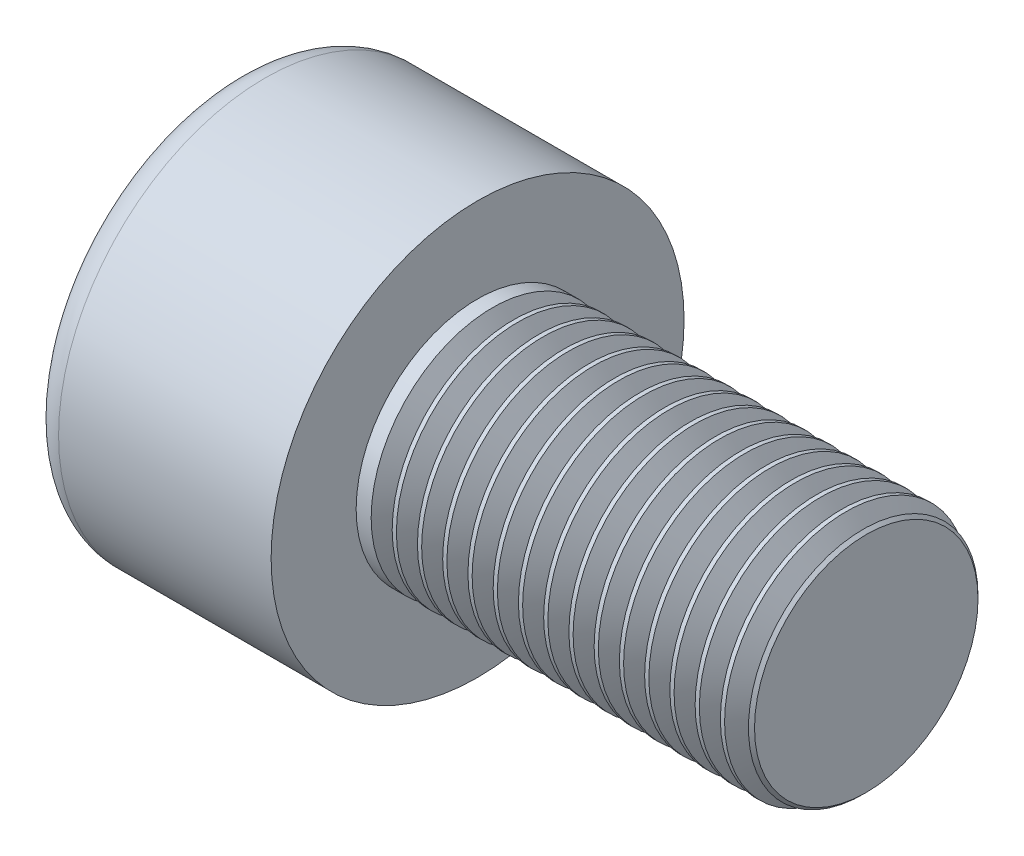
SolidWorks part; units mm, degrees
ref_plane "Front" through (0, 0, 0) normal (0, 0, 1) x (1, 0, 0)
ref_plane "Top" through (0, 0, 0) normal (0, 1, 0) x (1, 0, 0)
ref_plane "Right" through (0, 0, 0) normal (1, 0, 0) x (0, 0, -1)
sketch "Sketch1" plane through (0, 0, 0) normal (1, 0, 0) x (0, 0, -1)
  circle A0 centre (0, 0) radius 4.25
  dimension "dk" = 8.5
extrude "BaseHead" add sketch "Sketch1" along normal blind 5
sketch "Sketch2" plane through (5, 0, 0) normal (1, 0, 0) x (0, 0, -1)
  circle A0 centre (0, 0) radius 2.5
  dimension "d" = 5
extrude "BaseBody" add sketch "Sketch2" along normal blind 8
cosmetic thread "ThreadCosmetic1" parameters "b"=16, "D2"=4.134
sketch "Sketch3" plane through (0, 0, 0) normal (1, 0, 0) x (0, 0, -1)
  line L1 (2.3094, 0) -> (1.1547, 2)
  line L2 (1.1547, 2) -> (-1.1547, 2)
  line L3 (-1.1547, 2) -> (-2.3094, 0)
  line L4 (-2.3094, 0) -> (-1.1547, -2)
  line L5 (-1.1547, -2) -> (1.1547, -2)
  line L6 (1.1547, -2) -> (2.3094, 0)
  circle A0 centre (0, 0) radius 2 construction
  dimension "s" = 4
  dimension "e" = 4.6188
extrude "HexagonSocket" cut sketch "Sketch3" along normal blind 2.5
sketch "Sketch4" plane through (-4.1961, 0.75, 0) normal (0, 0, 1) x (-1, 0, 0)
  line L0 (-6.6961, 2.75) -> (-7.8508, 0.75)
  line L2 (-7.8508, 0.75) -> (-6.6961, 0.75)
  line L3 (-6.6961, 0.75) -> (-6.6961, 2.75)
  line L4 (-5.0351, 0.75) -> (0.839, 0.75) construction
  line L5 (-17.1961, 0.75) -> (-9.1961, 0.75) construction
  line L6 (-9.1961, 0.75) -> (-4.1961, 0.75) construction
  dimension "m" = 60
revolve "Cut-Revolve1" cut sketch "Sketch4" angle 360 about L4
fillet "HeadFillet" [suppressed] radius 0.2
fillet "TopFillet" radius 0.625 1 edges at (0, 0, -4.25)
chamfer "Chamfer1" distance 0.2 angle 45 1 edges at (13, 0, -2.5)
sketch "Sketch5" plane through (0, 0, 0) normal (0, 0, 1) x (1, 0, 0)
  line L0 (12.8, 2.125) -> (13.0165, 2.5)
  line L1 (13.0165, 2.5) -> (13.0165, 2.933)
  line L2 (13.0165, 2.933) -> (12.5835, 2.933)
  line L3 (12.5835, 2.933) -> (12.5835, 2.5)
  line L4 (12.5835, 2.5) -> (12.8, 2.125)
  line L5 (0, 0) -> (7.8886, 0) construction
  line L6 (12.8, -2.5) -> (12.8, 2.5) construction
  dimension "D1" = 5
  dimension "D2" = 0.433
revolve "Cut-Revolve10" cut sketch "Sketch5" angle 360 about L5
pattern_linear "LPattern10" count 15 spacing 0.5196 along (-1, 0, 0) of "Cut-Revolve10"
equation "\"r1@TopFillet\" = \"d@Sketch2\" / 8"
equation "\"D1@Chamfer1\" = \"r@HeadFillet\""
equation "\"D1@Sketch5\" = \"d@Sketch2\""
equation "\"D2@Sketch5\" =  ( \"d@Sketch2\" - \"D2@ThreadCosmetic1\" )  / 2"
equation "\"D3@LPattern10\" = \"D2@Sketch5\" * 1.2"
equation "\"D1@LPattern10\" = \"b@ThreadCosmetic1\" / \"D3@LPattern10\""
